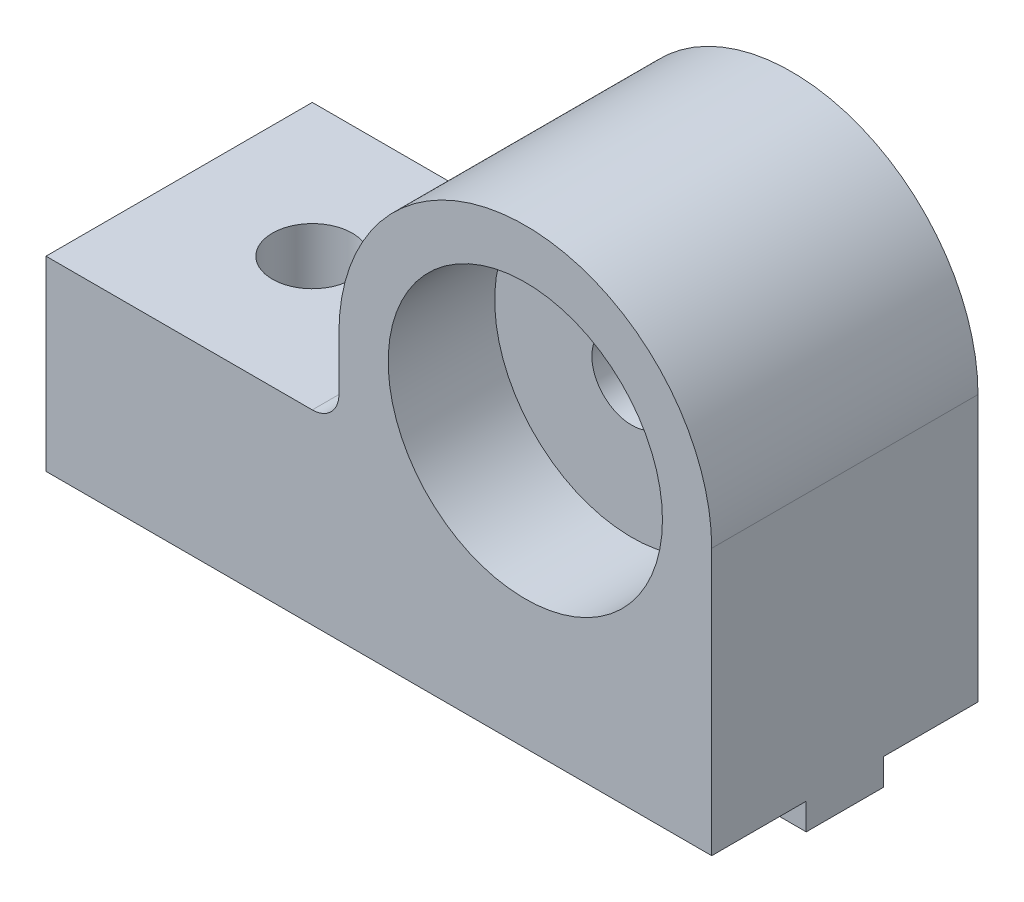
SolidWorks part; units mm, degrees
ref_plane "Front Plane" through (0, 0, 0) normal (0, 0, 1) x (1, 0, 0)
ref_plane "Top Plane" through (0, 0, 0) normal (0, 1, 0) x (1, 0, 0)
ref_plane "Right Plane" through (0, 0, 0) normal (1, 0, 0) x (0, 0, -1)
sketch "Sketch1" plane through (0, 0, 0) normal (0, 0, 1) x (1, 0, 0)
  line L0 (-18, 0) -> (7, 0)
  line L1 (7, 0) -> (7, 10)
  line L2 (-7, 10) -> (-7, 7)
  line L3 (-7, 7) -> (-18, 7)
  line L4 (-18, 7) -> (-18, 0)
  arc A0 (-7, 10) -> (7, 10) centre (0, 10) cw
  circle A1 centre (0, 10) radius 1.5
  dimension "D2" = 3
  dimension "D5" = 7
  dimension "D1" = 10
  dimension "D3" = 25
  dimension "D4" = 7
extrude "Main" add sketch "Sketch1" along normal mid plane 10
sketch "Sketch3" plane through (-18, 0, 0) normal (-1, 0, 0) x (0, 0, 1)
  line L0 (5, 0) -> (-5, 0) construction
  line L1 (-1.45, 0) -> (1.45, 0)
  line L2 (-1.45, 0) -> (-1.45, -1)
  line L3 (-1.45, -1) -> (1.45, -1)
  line L4 (1.45, 0) -> (1.45, -1)
  point P6 (0, -1)
  point P7 (0, 0)
  dimension "D1" = 1
  dimension "D2" = 2.9
extrude "MakerBeamRail" add sketch "Sketch3" against normal up to surface (25 mm away) up to face at (7, 5, 0)
sketch "Sketch2" plane through (0, 7, 0) normal (0, 1, 0) x (1, 0, 0)
  line L1 (-18, -5) -> (-18, 5) construction
  circle A0 centre (-13, 0) radius 1.5
  dimension "D1" = 3
  dimension "D2" = 5
extrude "MakerBeamFixHole" cut sketch "Sketch2" against normal through all
sketch "Sketch4" plane through (0, 0, 5) normal (0, 0, 1) x (1, 0, 0)
  circle A0 centre (0, 10) radius 5.15
  circle A1 centre (0, 10) radius 1.5 construction
  dimension "D1" = 10.3
extrude "RollingHole" cut sketch "Sketch4" against normal blind 4
mirror "MirrorRollingHole" about plane through (0, 0, 0) normal (0, 0, 1) of "RollingHole"
fillet "Fillet1" radius 1 1 edges at (-7, 7, 0)
